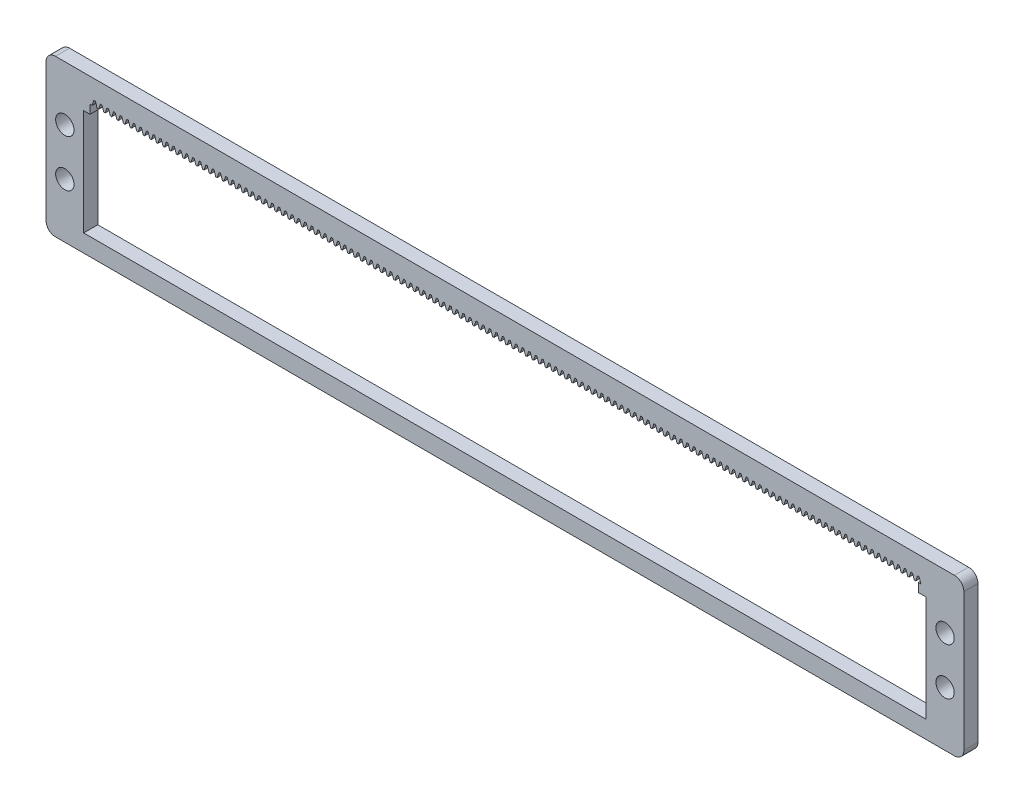
SolidWorks part; units mm, degrees
other "Markup1"
sketch "Sketch6" plane through (0, -30, 3.6) normal (0, 0, 1) x (1, 0, 0)
other "Markup2"
sketch "Sketch7" plane through (0, -30, 3.6) normal (0, 0, 1) x (1, 0, 0)
ref_plane "Front Plane" through (0, 0, 0) normal (0, 0, 1) x (1, 0, 0)
ref_plane "Top Plane" through (0, 0, 0) normal (0, 1, 0) x (1, 0, 0)
ref_plane "Right Plane" through (0, 0, 0) normal (1, 0, 0) x (0, 0, -1)
sketch "Sketch1" plane through (0, 0, 0) normal (0, 0, 1) x (1, 0, 0)
  line L1 (2, 0) -> (193, 0)
  line L2 (0, -2) -> (0, -31.22)
  line L3 (2, -33.22) -> (193, -33.22)
  line L4 (195, -2) -> (195, -31.22)
  arc A0 (193, -33.22) -> (195, -31.22) centre (193, -31.22) ccw
  arc A1 (0, -31.22) -> (2, -33.22) centre (2, -31.22) ccw
  arc A2 (2, 0) -> (0, -2) centre (2, -2) ccw
  arc A3 (193, 0) -> (195, -2) centre (193, -2) cw
  point P7 (195, -33.22)
  point P12 (0, 0)
  point P15 (195, 0)
  dimension "D3" = 2
  dimension "D1" = 33.22
  dimension "D2" = 195
extrude "Boss-Extrude1" add sketch "Sketch1" along normal blind 3
sketch "Sketch2" plane through (0, 0, 3) normal (0, 0, 1) x (1, 0, 0)
  line L0 (2, -33.22) -> (193, -33.22) construction
  line L1 (8, -7) -> (187, -7)
  line L2 (8, -7) -> (8, -29.5)
  line L3 (8, -29.5) -> (187, -29.5)
  line L4 (187, -7) -> (187, -29.5)
  line L5 (0, -2) -> (0, -31.22) construction
  line L7 (195, -31.22) -> (195, -2) construction
  line L8 (8, -18.25) -> (187, -18.25) construction
  line L12 (8, -29.5) -> (187, -29.5) construction
  line L13 (187, -4.3144) -> (187, -29.5) construction
  dimension "D1" = 22.5
  dimension "D2" = 8
  dimension "D3" = 8
  dimension "D4" = 3.72
extrude "Cut-Extrude1" cut sketch "Sketch2" against normal through all
sketch "Sketch3" plane through (0, 0, 3) normal (0, 0, 1) x (1, 0, 0)
  line L0 (187, -7) -> (8, -7) construction
  line L1 (9.35, -7) -> (185.32, -7)
  line L2 (9.35, -7) -> (9.35, -5.15)
  line L3 (9.35, -5.15) -> (185.32, -5.15)
  line L4 (185.32, -7) -> (185.32, -5.15)
  line L5 (187, -29.5) -> (187, -7) construction
  line L6 (8, -7) -> (8, -29.5) construction
  dimension "D1" = 1.85
  dimension "D2" = 1.68
  dimension "D3" = 1.35
extrude "Cut-Extrude2" cut sketch "Sketch3" against normal through all
sketch "Sketch4" plane through (0, 0, 3) normal (0, 0, 1) x (1, 0, 0)
  line L0 (186.345, -5.15) -> (185.865, -5.15) construction
  line L1 (185.32, -5.15) -> (9.35, -5.15) construction
  line L2 (186.345, -5.15) -> (186.725, -4.0118) construction
  line L3 (186.725, -4.0118) -> (185.485, -4.0118) construction
  line L4 (185.485, -4.0118) -> (185.865, -5.15)
  line L5 (185.485, -4.0118) -> (185.155, -4.0118)
  line L6 (185.155, -4.0118) -> (184.775, -5.15)
  line L7 (184.775, -5.15) -> (185.865, -5.15)
  line L10 (185.865, -5.15) -> (186.345, -5.15) construction
  dimension "D1" = 0.48
  dimension "D2" = 1.2
  dimension "D3" = 1.2
  dimension "D4" = 0.33
  dimension "D5" = 1.24
  dimension "D6" = 1.2
extrude "Cut-Extrude4" cut sketch "Sketch4" against normal through all
pattern_linear "LPattern1" count 126 spacing 1.4 along (-1, 0, 0) of "Cut-Extrude4"
sketch "Sketch5" plane through (0, 0, 3) normal (0, 0, 1) x (1, 0, 0)
  line L0 (187, -16.61) -> (195, -16.61) construction
  line L1 (193, 0) -> (2, 0) construction
  line L2 (8, -7) -> (8, -29.5) construction
  line L3 (0, -2) -> (0, -31.22) construction
  line L4 (2, -33.22) -> (193, -33.22) construction
  line L5 (0, -16.61) -> (8, -16.61) construction
  line L7 (191, -11.61) -> (191, -21.61) construction
  line L8 (4, -11.61) -> (4, -21.61) construction
  line L9 (187, -29.5) -> (187, -7) construction
  line L10 (195, -31.22) -> (195, -2) construction
  circle A4 centre (4, -11.61) radius 1.95
  circle A5 centre (4, -21.61) radius 1.95
  circle A6 centre (191, -11.61) radius 1.95
  circle A7 centre (191, -21.61) radius 1.95
  point P8 (191, -16.61)
  point P31 (191, -16.61)
  dimension "D1" = 3.9
  dimension "D2" = 4
  dimension "D3" = 3.9
  dimension "D4" = 3.9
  dimension "D6" = 3.9
  dimension "D5" = 10
  dimension "D7" = 10
extrude "Cut-Extrude5" cut sketch "Sketch5" against normal blind 10
